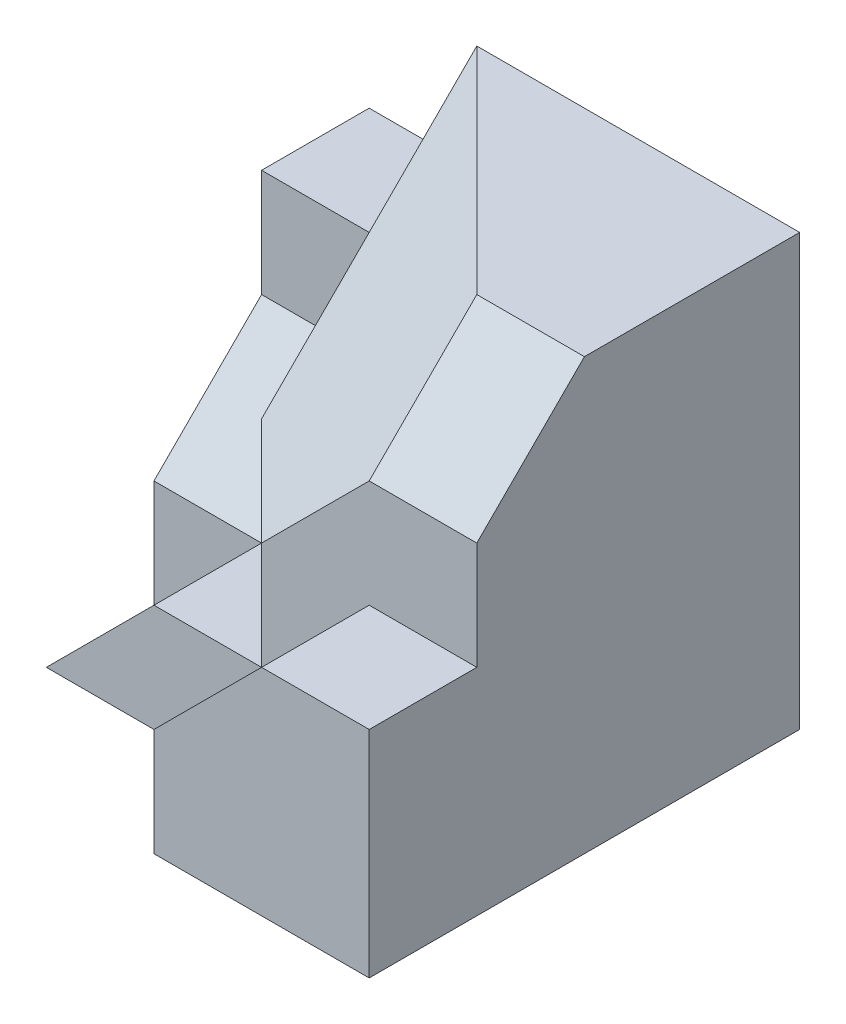
SolidWorks part; units mm, degrees
ref_plane "Front Plane" through (0, 0, 0) normal (0, 0, 1) x (1, 0, 0)
ref_plane "Top Plane" through (0, 0, 0) normal (0, 1, 0) x (1, 0, 0)
ref_plane "Right Plane" through (0, 0, 0) normal (1, 0, 0) x (0, 0, -1)
sketch "Sketch1" plane through (0, 0, 0) normal (0, 1, 0) x (1, 0, 0)
  line L0 (-15, 0) -> (0, 0)
  line L1 (0, 0) -> (0, -15)
  line L2 (0, -15) -> (-5, -15)
  line L3 (-5, -15) -> (-5, -10)
  line L4 (-5, -10) -> (-15, 0)
  dimension "D1" = 5
  dimension "D2" = 5
  dimension "D3" = 15
  dimension "D4" = 15
extrude "Boss-Extrude1" add sketch "Sketch1" along normal blind 20
sketch "Sketch8" plane through (-5, 0, 0) normal (-1, 0, 0) x (0, 0, 1)
  line L0 (10, 20) -> (15, 15)
  line L1 (15, 20) -> (15, 0) construction
  line L2 (15, 15) -> (15, 20)
  line L3 (15, 20) -> (10, 20)
  line L4 (0, 20) -> (10, 20) construction
  dimension "D1" = 5
extrude "Cut-Extrude5" cut sketch "Sketch8" against normal blind 30
ref_plane "Plane2" through (0, 0, 0) normal (0, -1, 0) x (-1, 0, 0)
sketch "Sketch9" plane through (0, 0, 0) normal (0, -1, 0) x (-1, 0, 0)
  line L0 (15, 0) -> (5, -10)
  line L1 (5, -10) -> (5, -15)
  line L2 (5, -15) -> (15, -15)
  line L3 (15, -15) -> (15, 0)
extrude "Boss-Extrude5" add sketch "Sketch9" against normal blind 20
sketch3d "3DSketch3"
  line L0 (-5, 20, 10) -> (-5, 15, 15) construction
  line L1 (-5, 20, 15) -> (-15, 20, 15) construction
  line L2 (-15, 20, 15) -> (-15, 20, 0) construction
  line L3 (-15, 20, 15) -> (-15, 0, 15) construction
  line L4 (-15, 20, 0) -> (-5, 20, 10)
  line L5 (-5, 20, 10) -> (-5, 15, 15)
  line L6 (-5, 15, 15) -> (-10, 10, 15)
  line L7 (-10, 10, 15) -> (-15, 10, 10)
  line L8 (-15, 10, 10) -> (-15, 20, 0)
  point P0 (-15, 20, 0)
  point P1 (-5, 20, 10)
  point P3 (-5, 15, 15)
  point P6 (-10, 10, 15)
  point P9 (-15, 10, 10)
  dimension "D1" = 10
  dimension "D2" = 10
  dimension "D3" = 5
  dimension "D4" = 5
extrude "Cut-Extrude9" cut sketch "3DSketch3" along direction (0, 0, -1) on the side of the normal blind 22
sketch "Sketch11" plane through (0, 10, 0) normal (0, 1, 0) x (1, 0, 0)
  line L0 (-15, -10) -> (-10, -15)
  line L1 (-10, -15) -> (-15, -15)
  line L2 (-15, -15) -> (-15, -10)
extrude "Cut-Extrude10" cut sketch "Sketch11" against normal blind 22
sketch "Sketch12" plane through (0, 0, 15) normal (0, 0, 1) x (1, 0, 0)
  line L0 (-5, 10) -> (0, 10)
  line L1 (0, 15) -> (0, 0) construction
  line L2 (0, 10) -> (0, 0)
  line L3 (0, 0) -> (-10, 0)
  line L4 (-10, 0) -> (-10, 5)
  line L5 (-10, 0) -> (-10, 10) construction
  line L6 (-10, 5) -> (-5, 10)
  dimension "D1" = 5
  dimension "D2" = 10
  dimension "D3" = 5
extrude "Boss-Extrude6" add sketch "Sketch12" along normal blind 5
sketch "Sketch13" plane through (-15, 0, 0) normal (-1, 0, 0) x (0, 0, 1)
  line L0 (0, 0) -> (0, 15)
  line L1 (0, 20) -> (0, 0) construction
  line L2 (0, 15) -> (5, 15)
  line L3 (5, 15) -> (5, 10)
  line L4 (5, 10) -> (10, 5)
  line L5 (10, 5) -> (10, 0)
  line L6 (10, 0) -> (0, 0)
  dimension "D1" = 10
  dimension "D2" = 5
  dimension "D3" = 5
  dimension "D4" = 5
  dimension "D5" = 10
extrude "Boss-Extrude7" add sketch "Sketch13" along normal blind 5
sketch "Sketch14" plane through (0, 0, 0) normal (0, -1, 0) x (-1, 0, 0)
  line L0 (20, -10) -> (15, -10)
  line L1 (15, -10) -> (10, -15)
  line L2 (10, -15) -> (20, -15)
  line L3 (20, -15) -> (20, -10)
  line L4 (20, 0) -> (20, -10) construction
  dimension "D1" = 10
extrude "Boss-Extrude8" add sketch "Sketch14" against normal blind 5
sketch "Sketch15" plane through (0, 0, 15) normal (0, 0, 1) x (1, 0, 0)
  line L0 (-20, 0) -> (-20, 5)
  line L1 (-20, 5) -> (-15, 5)
  line L2 (-10, 5) -> (-20, 5) construction
  line L3 (-15, 5) -> (-20, 0)
extrude "Cut-Extrude11" cut sketch "Sketch15" against normal blind 5
